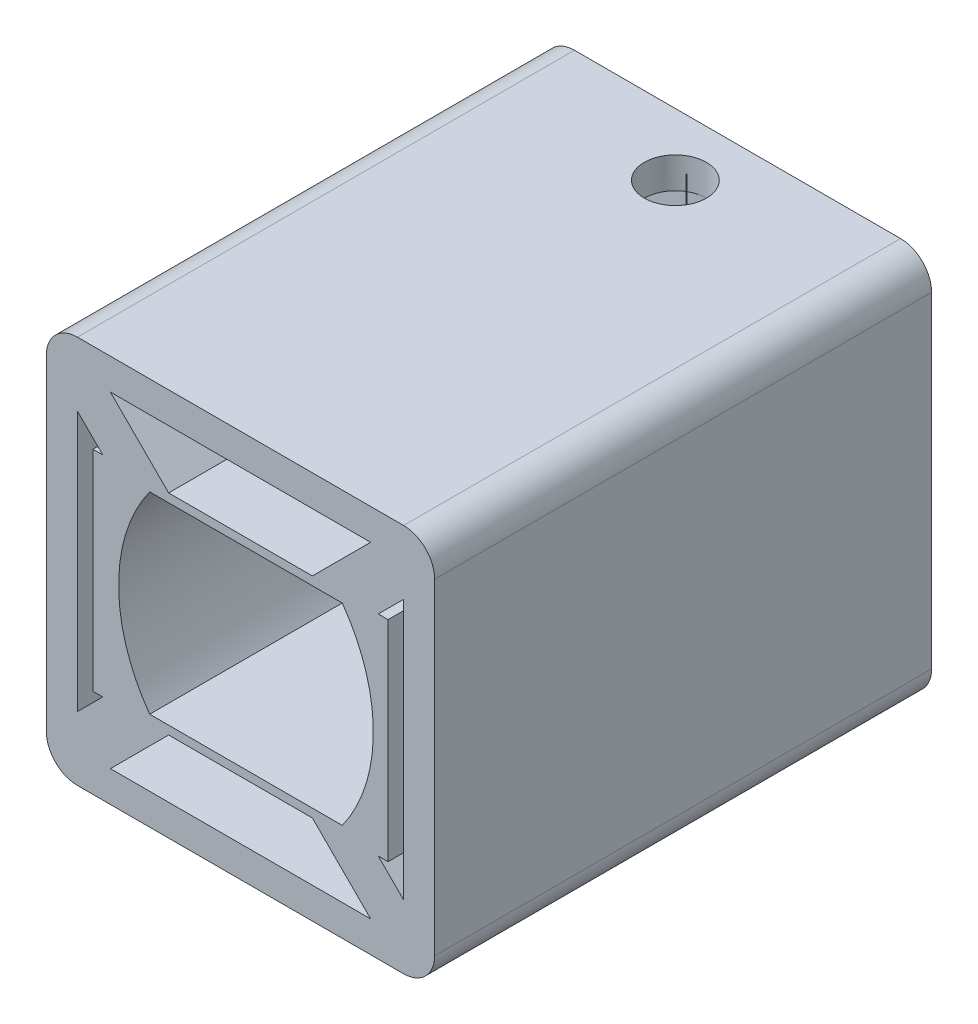
SolidWorks part; units mm, degrees
material "PLA"
ref_plane "Front Plane" through (0, 0, 0) normal (0, 0, 1) x (1, 0, 0)
ref_plane "Top Plane" through (0, 0, 0) normal (0, 1, 0) x (1, 0, 0)
ref_plane "Right Plane" through (0, 0, 0) normal (1, 0, 0) x (0, 0, -1)
sketch "Sketch1" plane through (0, 0, 0) normal (0, 0, 1) x (1, 0, 0)
  line L1 (-12.5, -12.5) -> (12.5, -12.5)
  line L2 (-12.5, -12.5) -> (-12.5, 12.5)
  line L3 (-12.5, 12.5) -> (12.5, 12.5)
  line L4 (12.5, -12.5) -> (12.5, 12.5)
  line L5 (-12.5, -12.5) -> (12.5, 12.5) construction
  line L6 (-12.5, 12.5) -> (12.5, -12.5) construction
  point P0 (0, 0)
  dimension "D1" = 25
sketch "Sketch2" plane through (0, 0, 0) normal (0, 0, 1) x (1, 0, 0)
  line L5 (-12.5, -12.5) -> (12.5, 12.5) construction
  line L6 (-12.5, 12.5) -> (12.5, -12.5) construction
  circle A0 centre (0, 0) radius 2.5
  circle A1 centre (8.25, 0) radius 1.425
  circle A2 centre (0, -8.25) radius 1.425
  circle A3 centre (-8.25, 0) radius 1.425
  circle A4 centre (0, 8.25) radius 1.425
  point P0 (0, 0)
  dimension "D2" = 4
  dimension "D1" = 25
extrude "Boss-Extrude1" add sketch "Sketch1" along normal blind 32
shell "Shell1" thickness 2
extrude "Cut-Extrude4" cut sketch "Sketch2" along normal blind 2
sketch "Sketch4" plane through (0, 0, 2) normal (0, 0, 1) x (1, 0, 0)
  line L0 (0.3516, 0) -> (-7.8484, 0)
  line L1 (-5.8484, -6.2) -> (6.5516, -6.2)
  line L3 (-5.8484, 6.2) -> (6.5516, 6.2)
  line L5 (-5.8484, -6.2) -> (6.5516, 6.2) construction
  line L6 (-5.8484, 6.2) -> (6.5516, -6.2) construction
  line L7 (0.3516, 0) -> (8.5516, 0)
  line L8 (0.3516, 0) -> (0.3516, 6.2)
  line L9 (0.3516, 0) -> (0.3516, -6.2)
  line L11 (-10.5, 8.3787) -> (8.3787, -10.5)
  line L12 (-10.5, -10.5) -> (10.5, -10.5) construction
  line L13 (-8.3787, 10.5) -> (10.5, -8.3787)
  line L14 (10.5, -10.5) -> (10.5, 10.5) construction
  line L15 (-10.5, -8.3787) -> (8.3787, 10.5)
  line L16 (10.5, 10.5) -> (-10.5, 10.5) construction
  line L17 (-8.3787, -10.5) -> (10.5, 8.3787)
  line L19 (-9.5, -6.75) -> (9.5, -6.75)
  line L20 (-9.5, -6.75) -> (-9.5, 6.75)
  line L21 (-9.5, 6.75) -> (9.5, 6.75)
  line L22 (9.5, -6.75) -> (9.5, 6.75)
  line L23 (-9.5, -6.75) -> (9.5, 6.75) construction
  line L24 (-9.5, 6.75) -> (9.5, -6.75) construction
  arc A2 (-5.8484, -6.2) -> (-5.8484, 6.2) centre (2.7616, 0) cw
  arc A3 (6.5516, 6.2) -> (6.5516, -6.2) centre (-2.0584, 0) cw
  point P0 (0, 0)
  point P12 (0, 0)
  point P22 (0, 0)
  point P25 (0, 0)
  point P28 (0, 0)
  point P33 (-1.0607, -1.0607)
  point P38 (1.0607, 1.0607)
  point P43 (-1.0607, 1.0607)
  point P46 (1.0607, -1.0607)
  circle M9 centre (8.25, 0) radius 1.425
  circle M11 centre (-8.25, 0) radius 1.425
  line M13 (10.5, -10.5) -> (10.5, 10.5)
  line M14 (10.5, 10.5) -> (-10.5, 10.5)
  line M15 (-10.5, 10.5) -> (-10.5, -10.5)
  line M16 (-10.5, -10.5) -> (10.5, -10.5)
  dimension "D1" = 19
extrude "Boss-Extrude3" add sketch "Sketch4" along normal blind 30 contours L11 A2 L3 L13 L21 | L11 L21 L13 M14 M15 | L21 L13 L3 L15 | L15 L21 L17 M13 M14 | L3 A3 L17 L21 L15 | L1 A2 L15 L19 L17 | L13 A3 L1 L11 L19 | L19 L15 L17 M15 M16 | L19 L11 L13 M16 M13 | L17 A3 L22 L21 M9 | A3 L13 L19 L22 M9 | L17 L19 L11 L1 | L15 A2 L20 L19 M11 | A2 L11 L21 L20 M11 | A2 L20 M11 | A3 L22 M9
sketch "Sketch5" plane through (0, 12.5, 0) normal (0, 1, 0) x (1, 0, 0)
  line L0 (0, 0) -> (0, -4)
  circle A0 centre (0.0246, -3.3013) radius 0.0246
  circle A1 centre (0, -4) radius 2
extrude "Cut-Extrude6" cut sketch "Sketch5" against normal blind 7.5
fillet "Fillet1" radius 2 4 edges at (-12.5, -12.5, 16) (12.5, 12.5, 16) (12.5, -12.5, 16) (-12.5, 12.5, 16)
